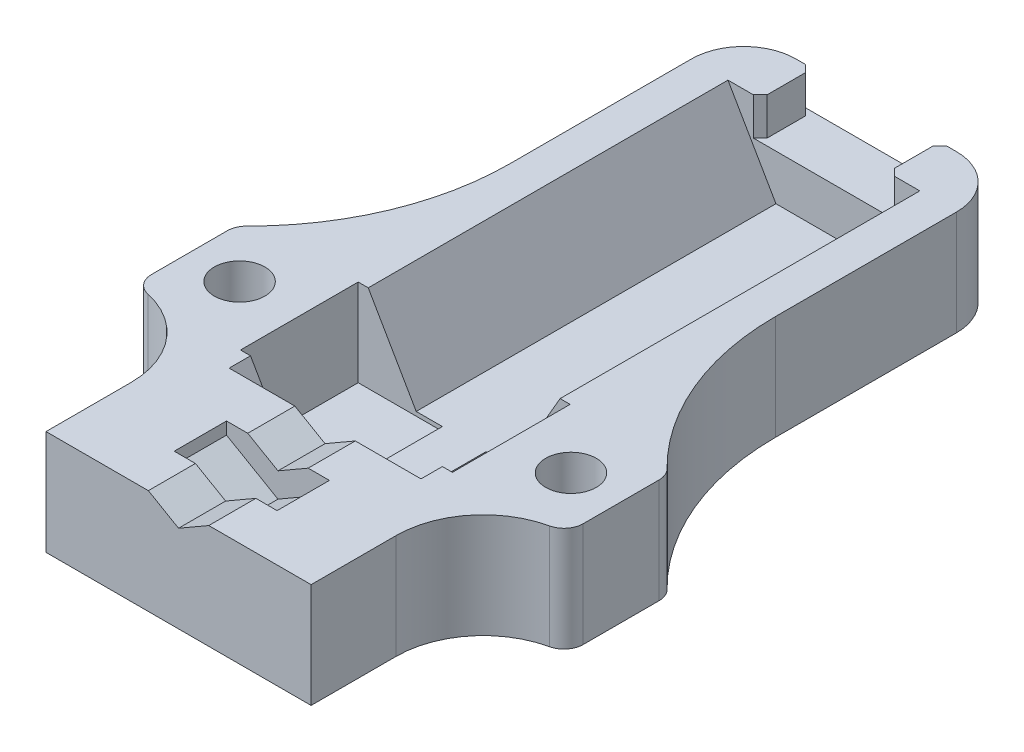
SolidWorks part; units mm, degrees
ref_plane "Plano frontal" through (0, 0, 0) normal (0, 0, 1) x (1, 0, 0)
ref_plane "Plano superior" through (0, 0, 0) normal (0, 1, 0) x (1, 0, 0)
ref_plane "Plano direito" through (0, 0, 0) normal (1, 0, 0) x (0, 0, -1)
sketch "Esboço1" plane through (0, 0, 0) normal (0, 1, 0) x (1, 0, 0)
  line L8 (-11.6295, -53.1294) -> (-11.6295, -58)
  line L9 (-16.4045, -42.825) -> (-16.4045, -47.175)
  line L11 (0.5705, -18) -> (-8.6295, -18)
  line L12 (3.5705, -31.3815) -> (3.5705, -21)
  line L13 (8.3455, -47.175) -> (8.3455, -42.825)
  line L17 (-16.4045, -42.825) -> (-16.4045, -47.175)
  line L19 (0.5705, -18) -> (-8.6295, -18)
  line L20 (3.5705, -31.3815) -> (3.5705, -21)
  line L21 (8.3455, -47.175) -> (8.3455, -42.825)
  line L40 (-11.6295, -21) -> (-11.6295, -31.3815)
  line L42 (-11.6295, -21) -> (-11.6295, -31.3815)
  line L44 (3.5705, -58) -> (3.5705, -53.1294)
  line L45 (3.5705, -58) -> (3.5705, -53.1294)
  line L46 (-11.6295, -58) -> (3.5705, -58)
  line L47 (-11.6295, -58) -> (3.5705, -58)
  line L129 (-11.6295, -53.1294) -> (-11.6295, -58)
  arc A12 (-16.0783, -42.0431) -> (-16.4045, -42.825) centre (-15.3045, -42.825) ccw
  arc A13 (-16.0783, -42.0431) -> (-11.6295, -31.3815) centre (-26.6295, -31.3815) ccw
  arc A14 (-8.6295, -18) -> (-11.6295, -21) centre (-8.6295, -21) ccw
  arc A15 (3.5705, -21) -> (0.5705, -18) centre (0.5705, -21) ccw
  arc A16 (3.5705, -31.3815) -> (8.0193, -42.0431) centre (18.5705, -31.3815) ccw
  arc A17 (8.3455, -42.825) -> (8.0193, -42.0431) centre (7.2455, -42.825) ccw
  arc A22 (-16.0783, -42.0431) -> (-16.4045, -42.825) centre (-15.3045, -42.825) ccw
  arc A23 (-16.0783, -42.0431) -> (-11.6295, -31.3815) centre (-26.6295, -31.3815) ccw
  arc A24 (-8.6295, -18) -> (-11.6295, -21) centre (-8.6295, -21) ccw
  arc A25 (3.5705, -21) -> (0.5705, -18) centre (0.5705, -21) ccw
  arc A26 (3.5705, -31.3815) -> (8.0193, -42.0431) centre (18.5705, -31.3815) ccw
  arc A27 (8.3455, -42.825) -> (8.0193, -42.0431) centre (7.2455, -42.825) ccw
  arc A32 (-16.4045, -47.175) -> (-15.5434, -48.2487) centre (-15.3045, -47.175) ccw
  arc A33 (-16.4045, -47.175) -> (-15.5434, -48.2487) centre (-15.3045, -47.175) ccw
  arc A34 (7.4844, -48.2487) -> (8.3455, -47.175) centre (7.2455, -47.175) ccw
  arc A35 (7.4844, -48.2487) -> (8.3455, -47.175) centre (7.2455, -47.175) ccw
  arc A36 (-11.6295, -53.1294) -> (-15.5434, -48.2487) centre (-16.6295, -53.1294) ccw
  arc A37 (-11.6295, -53.1294) -> (-15.5434, -48.2487) centre (-16.6295, -53.1294) ccw
  arc A38 (7.4844, -48.2487) -> (3.5705, -53.1294) centre (8.5705, -53.1294) ccw
  arc A39 (7.4844, -48.2487) -> (3.5705, -53.1294) centre (8.5705, -53.1294) ccw
  dimension "D1" = 0
sketch "Esboço2" plane through (0, -4.5495, 0) normal (0, -1, 0) x (1, 0, 0)
  line L6 (-11.6295, 31.3815) -> (-11.6295, 21)
  line L8 (8.3455, 42.825) -> (8.3455, 47.175)
  line L9 (3.5705, 21) -> (3.5705, 31.3815)
  line L10 (-8.6295, 18) -> (0.5705, 18)
  line L12 (-16.4045, 47.175) -> (-16.4045, 42.825)
  line L13 (-11.6295, 58) -> (-11.6295, 53.1294)
  line L16 (8.3455, 42.825) -> (8.3455, 47.175)
  line L17 (3.5705, 21) -> (3.5705, 31.3815)
  line L18 (-8.6295, 18) -> (0.5705, 18)
  line L20 (-16.4045, 47.175) -> (-16.4045, 42.825)
  line L37 (-11.6295, 58) -> (-11.6295, 53.1294)
  line L38 (-11.6295, 31.3815) -> (-11.6295, 21)
  line L39 (3.5705, 58) -> (-11.6295, 58)
  line L40 (3.5705, 58) -> (-11.6295, 58)
  line L41 (3.5705, 53.1294) -> (3.5705, 58)
  line L42 (3.5705, 53.1294) -> (3.5705, 58)
  circle A0 centre (5.4705, 45) radius 1.6 construction
  circle A1 centre (-13.5295, 45) radius 1.6 construction
  circle A2 centre (5.4705, 45) radius 1.6
  circle A3 centre (-13.5295, 45) radius 1.6
  arc A10 (8.0193, 42.0431) -> (8.3455, 42.825) centre (7.2455, 42.825) ccw
  arc A11 (8.0193, 42.0431) -> (3.5705, 31.3815) centre (18.5705, 31.3815) ccw
  arc A12 (0.5705, 18) -> (3.5705, 21) centre (0.5705, 21) ccw
  arc A13 (-11.6295, 21) -> (-8.6295, 18) centre (-8.6295, 21) ccw
  arc A14 (-11.6295, 31.3815) -> (-16.0783, 42.0431) centre (-26.6295, 31.3815) ccw
  arc A15 (-16.4045, 42.825) -> (-16.0783, 42.0431) centre (-15.3045, 42.825) ccw
  arc A20 (8.0193, 42.0431) -> (8.3455, 42.825) centre (7.2455, 42.825) ccw
  arc A21 (8.0193, 42.0431) -> (3.5705, 31.3815) centre (18.5705, 31.3815) ccw
  arc A22 (0.5705, 18) -> (3.5705, 21) centre (0.5705, 21) ccw
  arc A23 (-11.6295, 21) -> (-8.6295, 18) centre (-8.6295, 21) ccw
  arc A24 (-11.6295, 31.3815) -> (-16.0783, 42.0431) centre (-26.6295, 31.3815) ccw
  arc A25 (-16.4045, 42.825) -> (-16.0783, 42.0431) centre (-15.3045, 42.825) ccw
  arc A26 (-15.5434, 48.2487) -> (-16.4045, 47.175) centre (-15.3045, 47.175) ccw
  arc A27 (-15.5434, 48.2487) -> (-16.4045, 47.175) centre (-15.3045, 47.175) ccw
  arc A28 (-15.5434, 48.2487) -> (-11.6295, 53.1294) centre (-16.6295, 53.1294) ccw
  arc A29 (-15.5434, 48.2487) -> (-11.6295, 53.1294) centre (-16.6295, 53.1294) ccw
  arc A30 (3.5705, 53.1294) -> (7.4844, 48.2487) centre (8.5705, 53.1294) ccw
  arc A31 (3.5705, 53.1294) -> (7.4844, 48.2487) centre (8.5705, 53.1294) ccw
  arc A32 (8.3455, 47.175) -> (7.4844, 48.2487) centre (7.2455, 47.175) ccw
  arc A33 (8.3455, 47.175) -> (7.4844, 48.2487) centre (7.2455, 47.175) ccw
  dimension "D1" = 0
extrude "Ressalto-extrusão1" add sketch "Esboço2" along normal blind 6
sketch "Esboço3" plane through (0, -4.5495, 0) normal (0, -1, 0) x (1, 0, 0)
  line L0 (-10.1045, 41.625) -> (-5.2795, 41.625)
  line L1 (-5.2795, 41.625) -> (-5.2795, 48.375)
  line L2 (-5.2795, 48.375) -> (-10.1045, 48.375)
  line L3 (-10.1045, 48.375) -> (-10.1045, 41.625)
  line L4 (-2.6795, 48.275) -> (-2.6795, 41.725)
  line L5 (1.9455, 48.275) -> (-2.6795, 48.275)
  line L6 (1.9455, 41.725) -> (1.9455, 48.275)
  line L7 (-2.6795, 41.725) -> (1.9455, 41.725)
  line L8 (-2.6795, 48.275) -> (-2.6795, 41.725) construction
  line L9 (1.9455, 48.275) -> (-2.6795, 48.275) construction
  line L10 (1.9455, 41.725) -> (1.9455, 48.275) construction
  line L11 (-2.6795, 41.725) -> (1.9455, 41.725) construction
  line L12 (-10.0045, 48.275) -> (-10.0045, 41.725)
  line L13 (-5.3795, 48.275) -> (-10.0045, 48.275)
  line L14 (-5.3795, 41.725) -> (-5.3795, 48.275)
  line L15 (-10.0045, 41.725) -> (-5.3795, 41.725)
  line L16 (-10.0045, 48.275) -> (-10.0045, 41.725) construction
  line L17 (-5.3795, 48.275) -> (-10.0045, 48.275) construction
  line L18 (-5.3795, 41.725) -> (-5.3795, 48.275) construction
  line L19 (-10.0045, 41.725) -> (-5.3795, 41.725) construction
  line L20 (-2.7795, 41.625) -> (2.0455, 41.625)
  line L21 (2.0455, 41.625) -> (2.0455, 48.375)
  line L22 (2.0455, 48.375) -> (-2.7795, 48.375)
  line L23 (-2.7795, 48.375) -> (-2.7795, 41.625)
  dimension "D1" = 0
  dimension "D2" = 0
  dimension "D3" = 0.1
extrude "Corte-extrusão1" cut sketch "Esboço3" along normal offset from surface (5 mm away) 0.4
ref_plane "Plano2" through (-4.0295, 0, 0) normal (1, 0, 0) x (0, 0, -1)
ref_plane "Plano3" through (0, 0, 21) normal (0, 0, -1) x (-1, 0, 0)
sketch "Esboço15" plane through (0, 0, 18) normal (0, 0, -1) x (-1, 0, 0)
  line L0 (8.6295, -4.5495) -> (-0.5705, -4.5495) construction
  line L1 (9.5295, -4.5495) -> (6.7795, 0.2137)
  line L2 (6.7795, 0.2137) -> (1.2795, 0.2137)
  line L3 (1.2795, 0.2137) -> (-1.4705, -4.5495)
  line L4 (-1.4705, -4.5495) -> (1.2795, -9.3126)
  line L5 (1.2795, -9.3126) -> (6.7795, -9.3126)
  line L6 (6.7795, -9.3126) -> (9.5295, -4.5495)
  line L7 (-1.4705, -4.5495) -> (9.5295, -4.5495)
  circle A0 centre (4.0295, -4.5495) radius 5.5 construction
  dimension "D1" = 11
sketch "Esboço16" plane through (0, 0, 21) normal (0, 0, -1) x (-1, 0, 0)
  line L0 (9.5295, -4.5495) -> (6.7795, 0.2137) construction
  line L1 (6.7795, 0.2137) -> (1.2795, 0.2137) construction
  line L2 (1.2795, 0.2137) -> (-1.4705, -4.5495) construction
  line L3 (-1.4705, -4.5495) -> (1.2795, -9.3126) construction
  line L4 (1.2795, -9.3126) -> (6.7795, -9.3126) construction
  line L5 (6.7795, -9.3126) -> (9.5295, -4.5495) construction
  line L6 (-1.4705, -4.5495) -> (9.5295, -4.5495) construction
  line L7 (9.5295, -4.5495) -> (6.7795, 0.2137)
  line L8 (6.7795, 0.2137) -> (1.2795, 0.2137)
  line L9 (1.2795, 0.2137) -> (-1.4705, -4.5495)
  line L10 (-1.4705, -4.5495) -> (1.2795, -9.3126)
  line L11 (1.2795, -9.3126) -> (6.7795, -9.3126)
  line L12 (6.7795, -9.3126) -> (9.5295, -4.5495)
  line L13 (-1.4705, -4.5495) -> (9.5295, -4.5495)
extrude "Corte-extrusão10" cut sketch "Esboço16" against normal blind 28.6 contours L13 L10 L11 L12
sketch "Esboço18" plane through (0, 0, 18) normal (0, 0, -1) x (-1, 0, 0)
  line L0 (8.6295, -4.5495) -> (-0.5705, -4.5495) construction
  line L1 (7.6795, -4.5495) -> (0.3795, -4.5495)
  line L2 (7.6795, -4.5495) -> (7.6795, -6.6995)
  line L3 (7.6795, -6.6995) -> (0.3795, -6.6995)
  line L4 (0.3795, -4.5495) -> (0.3795, -6.6995)
  point P5 (4.0295, -4.5495)
  point P8 (4.0295, -4.5495)
  dimension "D1" = 7.3
  dimension "D2" = 2.15
extrude "Corte-extrusão13" cut sketch "Esboço18" against normal up to surface (3 mm away) up to face at (-4.0295, -6.931, 21)
sketch "Esboço19" plane through (0, -10.5495, 0) normal (0, -1, 0) x (1, 0, 0)
  circle A0 centre (5.4705, 45) radius 1.6 construction
  circle A1 centre (-13.5295, 45) radius 1.6 construction
  circle A2 centre (5.4705, 45) radius 1.6
  circle A3 centre (-13.5295, 45) radius 1.6
extrude "Ressalto-extrusão2" add sketch "Esboço19" against normal blind 1
sketch "Esboço25" plane through (0, -4.5495, 0) normal (0, 1, 0) x (1, 0, 0)
  circle A0 centre (-13.5295, -45) radius 1.6 construction
  circle A1 centre (5.4705, -45) radius 1.6 construction
  circle A10 centre (-13.5295, -45) radius 1.6
  circle A11 centre (5.4705, -45) radius 1.6
  circle A12 centre (5.4705, -45) radius 1.45
  circle A13 centre (-13.5295, -45) radius 1.45
  dimension "D1" = 0.15
extrude "Ressalto-extrusão3" add sketch "Esboço25" against normal up to surface (5 mm away) up to face at (-13.5295, -9.5495, 43.4)
chamfer "Chanfro1" distance 0.4 angle 45 4 edges at (-7.6795, -5.6245, 21) (-7.6795, -5.6245, 18) (-0.3795, -5.6245, 21) (-0.3795, -5.6245, 18)
ref_plane "Plano4" through (0, -5.6245, 0) normal (0, 1, 0) x (1, 0, 0)
sketch "Esboço27" plane through (0, -10.5495, 0) normal (0, -1, 0) x (1, 0, 0)
  line L1 (-4.0295, 58) -> (-4.0295, 18) construction
  line L2 (3.5705, 58) -> (-11.6295, 58) construction
  line L3 (-8.6295, 18) -> (0.5705, 18) construction
  arc A6 (-15.7911, 45.5948) -> (-10.7831, 37.4456) centre (-3.8463, 47.322) ccw
  arc A7 (-8.3896, 47.1213) -> (-9.4651, 37.7509) centre (-20.3593, 43.7482) cw
  arc A8 (-14.3178, 47.9238) -> (-10.6269, 48.6569) centre (-8.9266, 30.4399) cw
  arc A9 (-8.3896, 47.1213) -> (-10.6269, 48.6569) centre (-10.4299, 46.5464) ccw
  arc A10 (-15.7911, 45.5948) -> (-14.3178, 47.9238) centre (-13.6932, 45.8981) cw
  arc A11 (-9.4651, 37.7509) -> (-10.7831, 37.4456) centre (-10.2609, 38.189) cw
  arc A12 (-5.9007, 32.8717) -> (-9.649, 27.0801) centre (17.565, 13.5761) ccw
  arc A17 (-10.9358, 23.1114) -> (-9.649, 27.0801) centre (3.1024, 20.7527) cw
  arc A18 (-5.9007, 32.8717) -> (-2.1583, 32.8717) centre (-4.0295, 31.3331) cw
  arc A19 (-6.8152, 23.042) -> (-4.3978, 20.4154) centre (-1.9477, 25.0961) ccw
  arc A20 (-6.4831, 23.8394) -> (-1.5759, 23.8394) centre (-4.0295, 17.7341) cw
  arc A21 (-6.8152, 23.042) -> (-6.4831, 23.8394) centre (-6.2572, 23.2774) cw
  arc A22 (-10.9358, 23.1114) -> (-4.3978, 20.4154) centre (-7.3588, 22.5103) ccw
  arc A23 (-9.1479, 34.5398) -> (-6.3672, 34.5398) centre (-7.7575, 32.9524) cw
  arc A24 (-9.4272, 34.8587) -> (-6.0878, 34.8587) centre (-7.7575, 32.9524) cw
  arc A25 (-9.4272, 34.8587) -> (-9.1479, 34.5398) centre (-9.2875, 34.6992) ccw
  arc A26 (-6.3672, 34.5398) -> (-6.0878, 34.8587) centre (-6.2275, 34.6992) ccw
  arc A27 (-1.2438, 23.042) -> (-1.5759, 23.8394) centre (-1.8018, 23.2774) ccw
  arc A28 (-1.2438, 23.042) -> (-3.6612, 20.4154) centre (-6.1113, 25.0961) cw
  arc A29 (2.8768, 23.1114) -> (-3.6612, 20.4154) centre (-0.7002, 22.5103) cw
  arc A30 (2.8768, 23.1114) -> (1.59, 27.0801) centre (-11.1614, 20.7527) ccw
  arc A31 (-2.1583, 32.8717) -> (1.59, 27.0801) centre (-25.624, 13.5761) cw
  arc A32 (1.3682, 34.8587) -> (1.0889, 34.5398) centre (1.2285, 34.6992) cw
  arc A33 (1.3682, 34.8587) -> (-1.9711, 34.8587) centre (-0.3015, 32.9524) ccw
  arc A34 (-1.6918, 34.5398) -> (-1.9711, 34.8587) centre (-1.8315, 34.6992) cw
  arc A35 (1.0889, 34.5398) -> (-1.6918, 34.5398) centre (-0.3015, 32.9524) ccw
  arc A36 (7.7322, 45.5948) -> (6.2588, 47.9238) centre (5.6342, 45.8981) ccw
  arc A37 (6.2588, 47.9238) -> (2.5679, 48.6569) centre (0.8676, 30.4399) ccw
  arc A38 (0.3306, 47.1213) -> (2.5679, 48.6569) centre (2.3709, 46.5464) cw
  arc A39 (0.3306, 47.1213) -> (1.4061, 37.7509) centre (12.3004, 43.7482) ccw
  arc A40 (1.4061, 37.7509) -> (2.7241, 37.4456) centre (2.2019, 38.189) ccw
  arc A41 (7.7322, 45.5948) -> (2.7241, 37.4456) centre (-4.2127, 47.322) cw
  arc A42 (-8.8709, 46.9857) -> (-9.9031, 37.992) centre (-20.3593, 43.7482) cw
  arc A43 (-9.9031, 37.992) -> (-10.4957, 37.8547) centre (-10.2609, 38.189) cw
  arc A44 (-15.2963, 45.6663) -> (-10.4957, 37.8547) centre (-3.8463, 47.322) ccw
  arc A45 (-15.2963, 45.6663) -> (-14.1705, 47.446) centre (-13.6932, 45.8981) cw
  arc A46 (-14.1705, 47.446) -> (-10.5804, 48.1591) centre (-8.9266, 30.4399) cw
  arc A47 (-8.8709, 46.9857) -> (-10.5804, 48.1591) centre (-10.4299, 46.5464) ccw
  arc A48 (7.2373, 45.6663) -> (6.1115, 47.446) centre (5.6342, 45.8981) ccw
  arc A49 (6.1115, 47.446) -> (2.5214, 48.1591) centre (0.8676, 30.4399) ccw
  arc A50 (0.8119, 46.9857) -> (2.5214, 48.1591) centre (2.3709, 46.5464) cw
  arc A51 (0.8119, 46.9857) -> (1.8441, 37.992) centre (12.3004, 43.7482) ccw
  arc A52 (1.8441, 37.992) -> (2.4367, 37.8547) centre (2.2019, 38.189) ccw
  arc A53 (7.2373, 45.6663) -> (2.4367, 37.8547) centre (-4.2127, 47.322) cw
  arc A54 (-5.5145, 32.5541) -> (-2.5445, 32.5541) centre (-4.0295, 31.3331) cw
  arc A55 (-2.5445, 32.5541) -> (1.1421, 26.8579) centre (-25.624, 13.5761) cw
  arc A56 (2.3837, 23.0285) -> (1.1421, 26.8579) centre (-11.1614, 20.7527) ccw
  arc A57 (2.3837, 23.0285) -> (-2.8992, 20.2869) centre (-0.7002, 22.5103) cw
  arc A58 (-0.7831, 22.8476) -> (-2.8992, 20.2869) centre (-6.1113, 25.0961) cw
  arc A59 (-0.7831, 22.8476) -> (-1.3895, 24.3033) centre (-1.8018, 23.2774) ccw
  arc A60 (-6.6695, 24.3033) -> (-1.3895, 24.3033) centre (-4.0295, 17.7341) cw
  arc A61 (-7.2759, 22.8476) -> (-6.6695, 24.3033) centre (-6.2572, 23.2774) cw
  arc A62 (-7.2759, 22.8476) -> (-5.1598, 20.2869) centre (-1.9477, 25.0961) ccw
  arc A63 (-10.4427, 23.0285) -> (-5.1598, 20.2869) centre (-7.3588, 22.5103) ccw
  arc A64 (-10.4427, 23.0285) -> (-9.2011, 26.8579) centre (3.1024, 20.7527) cw
  arc A65 (-5.5145, 32.5541) -> (-9.2011, 26.8579) centre (17.565, 13.5761) ccw
  dimension "D1" = 0.5
extrude "Corte-extrusão16" cut sketch "Esboço27" against normal blind 0.3
sketch "Esboço28" plane through (0, -10.5495, 0) normal (0, -1, 0) x (1, 0, 0)
  line L1 (3.5705, 58) -> (-11.6295, 58) construction
  line L2 (-11.0295, 50.8) -> (2.9705, 50.8) construction
  line L4 (3.5705, 58) -> (-11.6295, 58) construction
  line L5 (-4.0295, 58) -> (-4.0295, 50.8) construction
  line L6 (-9.8352, 54) -> (1.7762, 54) construction
  text T0 "ggo" font "Swis721 BlkEx BT" height 3
  text T1 "Do" font "Swis721 BlkEx BT" height 3
  point P7 (-4.0295, 50.8)
  point P11 (-4.0295, 54)
  dimension "D1" = 14
  dimension "D2" = 4
  dimension "D3" = 7.2
extrude "Corte-extrusão17" cut sketch "Esboço28" against normal blind 0.3
sketch "Esboço29" plane through (-4.0295, -3.5495, 53.8) normal (0, 0, 1) x (0.866, 0.5, 0)
  line L6 (-3.4064, 0) -> (-1.7032, -2.95)
  line L7 (-1.7032, -2.95) -> (1.7032, -2.95)
  line L8 (1.7032, -2.95) -> (3.4064, 0)
  line L9 (3.4064, 0) -> (1.7032, 2.95)
  line L10 (1.7032, 2.95) -> (-1.7032, 2.95)
  line L11 (-1.7032, 2.95) -> (-3.4064, 0)
  line L12 (-3.4064, 0) -> (-1.7032, -2.95)
  line L13 (-1.7032, -2.95) -> (1.7032, -2.95)
  line L14 (1.7032, -2.95) -> (3.4064, 0)
  line L15 (3.4064, 0) -> (1.7032, 2.95)
  line L16 (1.7032, 2.95) -> (-1.7032, 2.95)
  line L17 (-1.7032, 2.95) -> (-3.4064, 0)
  dimension "D1" = 0
extrude "Corte-extrusão18" cut sketch "Esboço29" against normal mid plane 3
sketch "Esboço30" plane through (0, 0, 58) normal (0, 0, 1) x (1, 0, 0)
  line L6 (-4.0295, -5.5495) -> (-2.2974, -4.5495)
  line L7 (-2.2974, -4.5495) -> (-2.2974, -2.5495)
  line L8 (-2.2974, -2.5495) -> (-4.0295, -1.5495)
  line L9 (-4.0295, -1.5495) -> (-5.7615, -2.5495)
  line L10 (-5.7615, -2.5495) -> (-5.7615, -4.5495)
  line L11 (-5.7615, -4.5495) -> (-4.0295, -5.5495)
  line L12 (-4.0295, -5.5495) -> (-2.2974, -4.5495)
  line L13 (-2.2974, -4.5495) -> (-2.2974, -2.5495)
  line L14 (-2.2974, -2.5495) -> (-4.0295, -1.5495)
  line L15 (-4.0295, -1.5495) -> (-5.7615, -2.5495)
  line L16 (-5.7615, -2.5495) -> (-5.7615, -4.5495)
  line L17 (-5.7615, -4.5495) -> (-4.0295, -5.5495)
  dimension "D1" = 0
extrude "Corte-extrusão19" cut sketch "Esboço30" against normal up to surface (8.4 mm away) up to face at (-4.0295, -6.931, 49.6)
